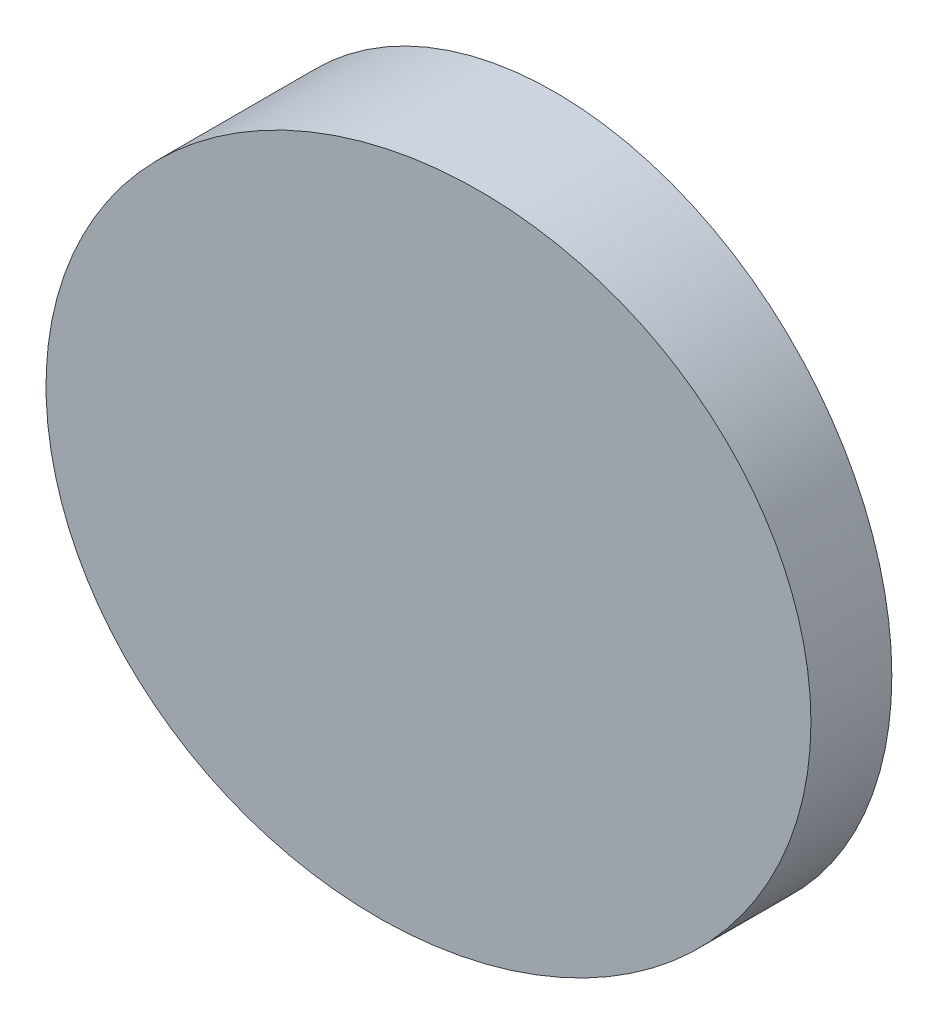
SolidWorks part; units mm, degrees
ref_plane "前视基准面" through (0, 0, 0) normal (0, 0, 1) x (1, 0, 0)
ref_plane "上视基准面" through (0, 0, 0) normal (0, 1, 0) x (1, 0, 0)
ref_plane "右视基准面" through (0, 0, 0) normal (1, 0, 0) x (0, 0, -1)
sketch "草图1" plane through (0, 0, 0) normal (0, 0, 1) x (1, 0, 0)
  circle A0 centre (0, 0) radius 12.5
extrude "凸台-拉伸1" add sketch "草图1" along normal blind 10
sketch "草图2" plane through (0, 0, 0) normal (0, 1, 0) x (1, 0, 0)
  line L0 (12.5, -3) -> (-16.3807, -6.8946)
  line L1 (12.5, -10) -> (12.5, 0) construction
  line L2 (-16.3807, -6.8946) -> (-16.3807, -17.8324)
  line L3 (-16.3807, -17.8324) -> (18.0281, -17.8324)
  line L4 (18.0281, -17.8324) -> (18.0281, -3)
  line L5 (18.0281, -3) -> (12.5, -3)
  line L6 (12.5, 0) -> (-12.5, 0) construction
  dimension "D1" = 7.68
  dimension "D2" = 3
extrude "切除-拉伸1" cut sketch "草图2" against normal mid plane 50
